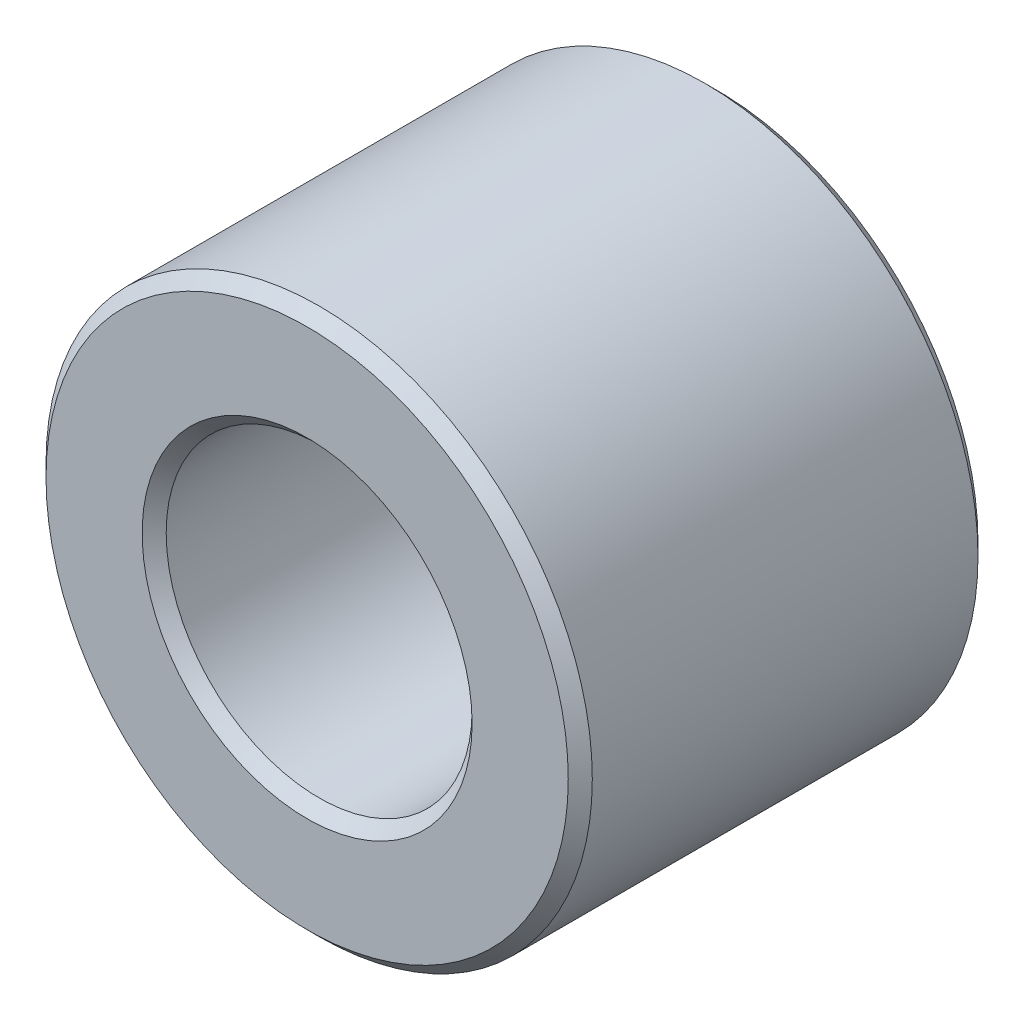
SolidWorks part; units mm, degrees
ref_plane "Front Plane" through (0, 0, 0) normal (0, 0, 1) x (1, 0, 0)
ref_plane "Top Plane" through (0, 0, 0) normal (0, 1, 0) x (1, 0, 0)
ref_plane "Right Plane" through (0, 0, 0) normal (1, 0, 0) x (0, 0, -1)
sketch "Sketch1" plane through (0, 0, 0) normal (0, 0, 1) x (1, 0, 0)
  circle A0 centre (0, 0) radius 3.175 construction
  circle A1 centre (0, 0) radius 1.778 construction
  point P4 (0, 3.175)
  dimension "ID" = 3.556
  dimension "OD" = 6.35
sketch "Sketch2" plane through (0, 0, 0) normal (1, 0, 0) x (0, 0, -1)
  line L0 (-2.3813, 3.175) -> (2.3813, 3.175) construction
  dimension "Length" = 4.7625
sketch "Sketch3" plane through (0, 0, 0) normal (0, 0, 1) x (1, 0, 0)
  circle A0 centre (0, 0) radius 1.778 construction
  circle A1 centre (0, 0) radius 3.175 construction
  circle A2 centre (0, 0) radius 1.778
  circle A3 centre (0, 0) radius 3.175
extrude "Boss-Extrude1" add sketch "Sketch3" against normal up to vertex (2.3813 mm away) and the other way up to vertex (2.3813 mm away) up to point (0, 3.175, -2.3813) other way up to point (0, 3.175, 2.3813)
chamfer "Chamfer1" distance 0.1397 angle 45 1 edges at (3.175, 0, 2.3813)
equation "\"D1@Chamfer1\"=(\"OD@Sketch1\"-\"ID@Sketch1\")*0.05"
